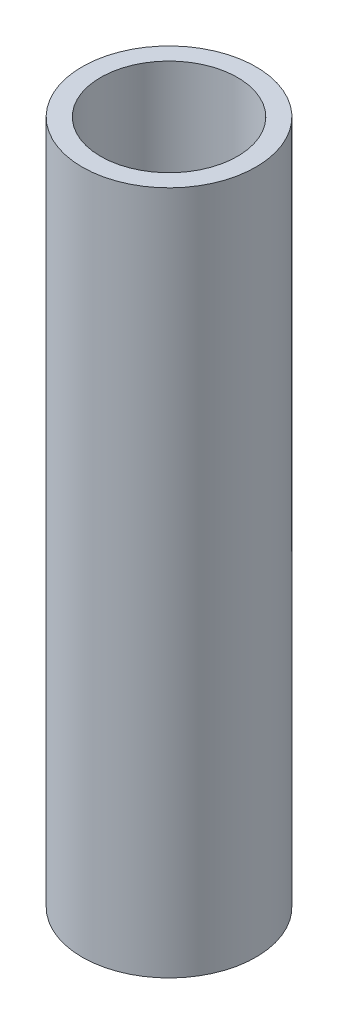
SolidWorks part; units mm, degrees
ref_plane "Plan de face" through (0, 0, 0) normal (0, 0, 1) x (1, 0, 0)
ref_plane "Plan de dessus" through (0, 0, 0) normal (0, 1, 0) x (1, 0, 0)
ref_plane "Plan de droite" through (0, 0, 0) normal (1, 0, 0) x (0, 0, -1)
sketch "Esquisse1" plane through (0, 0, 0) normal (0, 1, 0) x (1, 0, 0)
  circle A0 centre (0, 0) radius 5
  circle A1 centre (0, 0) radius 6.35
  dimension "D1" = 12.7
  dimension "D2" = 10
extrude "Boss.-Extru.1" add sketch "Esquisse1" along normal blind 50 contours A1 | A0
